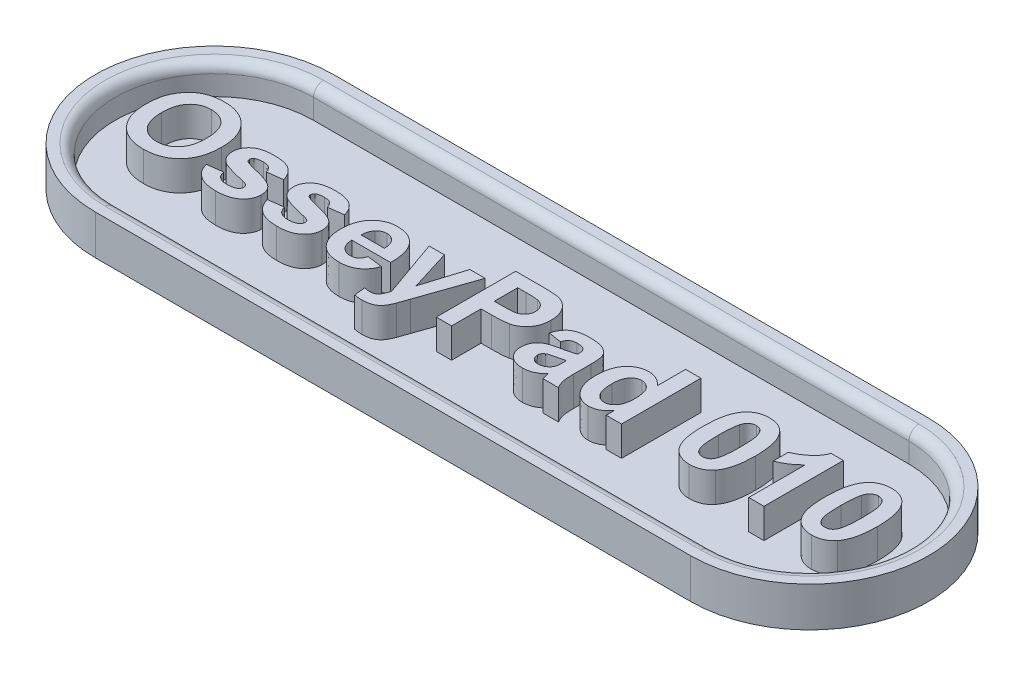
SolidWorks part; units mm, degrees
ref_plane "Front Plane" through (0, 0, 0) normal (0, 0, 1) x (1, 0, 0)
ref_plane "Top Plane" through (0, 0, 0) normal (0, 1, 0) x (1, 0, 0)
ref_plane "Right Plane" through (0, 0, 0) normal (1, 0, 0) x (0, 0, -1)
sketch "Sketch1" plane through (0, 0, 0) normal (0, 1, 0) x (1, 0, 0)
  line L0 (-15, 0) -> (15, 0) construction
  line L1 (-15, 6) -> (15, 6)
  line L2 (-15, -6) -> (15, -6)
  arc A0 (-15, 6) -> (-15, -6) centre (-15, 0) ccw
  arc A1 (15, -6) -> (15, 6) centre (15, 0) ccw
  point P2 (0, 0)
  dimension "D1" = 12
  dimension "D2" = 30
extrude "Boss-Extrude1" add sketch "Sketch1" along normal blind 2
sketch "Sketch2" plane through (0, 2, 0) normal (0, 1, 0) x (1, 0, 0)
  line L0 (-15, 0) -> (15, 0) construction
  line L1 (-15, 5) -> (15, 5)
  line L2 (-15, -5) -> (15, -5)
  arc A0 (-15, 5) -> (-15, -5) centre (-15, 0) ccw
  arc A1 (15, -5) -> (15, 5) centre (15, 0) ccw
  point P2 (0, 0)
  dimension "D1" = 30
  dimension "D2" = 10
extrude "Cut-Extrude1" cut sketch "Sketch2" against normal blind 1.5
sketch "Sketch3" plane through (0, 0.5, 0) normal (0, 1, 0) x (1, 0, 0)
  line L0 (-21, -1.995) -> (21, -1.995) construction
  line L1 (0, -8.7006) -> (0, 6.9821) construction
  line L3 (-15, -5) -> (15, -5) construction
  text T0 "OsseyPad 010" font "Arial" height 4
  dimension "D1" = 3.005
extrude "Boss-Extrude2" add sketch "Sketch3" along normal blind 1.5
fillet "Fillet1" radius 0.5 4 edges at (0, 2, -5) (20, 2, 0) (0, 2, 5) (-20, 2, 0)
